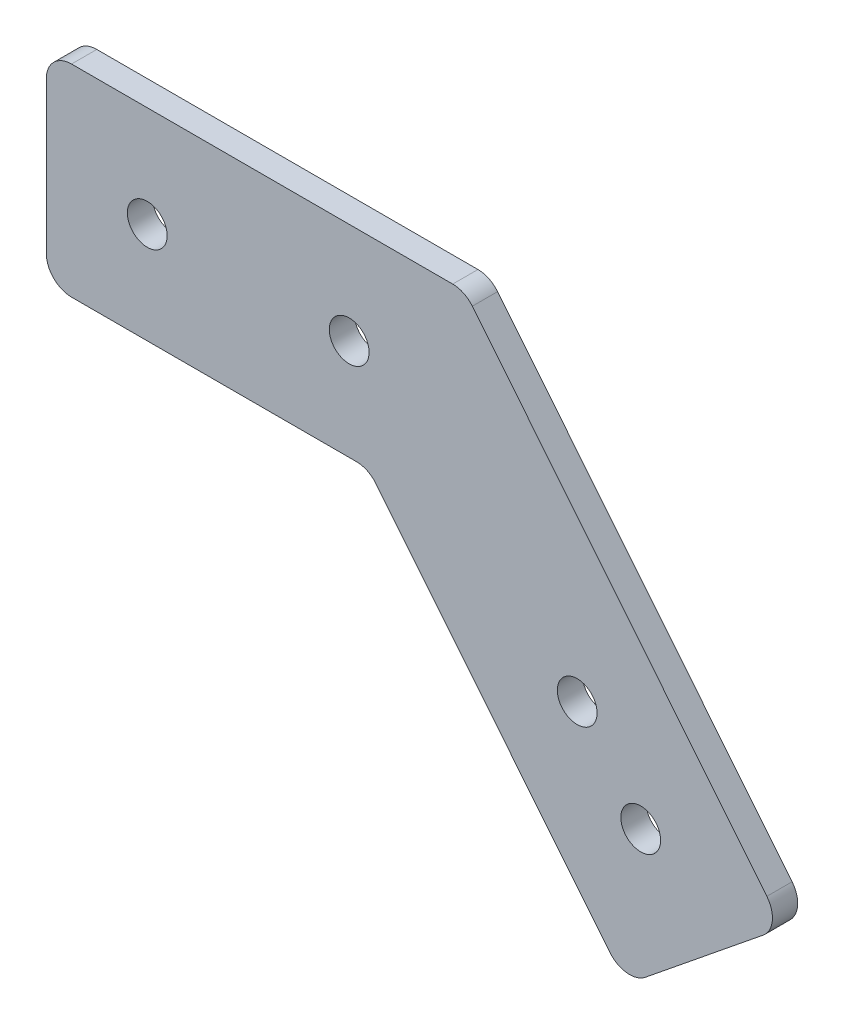
SolidWorks part; units mm, degrees
ref_plane "Front Plane" through (0, 0, 0) normal (0, 0, 1) x (1, 0, 0)
ref_plane "Top Plane" through (0, 0, 0) normal (0, 1, 0) x (1, 0, 0)
ref_plane "Right Plane" through (0, 0, 0) normal (1, 0, 0) x (0, 0, -1)
sketch "Sketch1" plane through (0, 0, 0) normal (0, 0, 1) x (1, 0, 0)
  line L0 (72.8931, 668.9416) -> (92.6349, 684.9236)
  line L1 (50.8, 696.2321) -> (635, -25.4) construction
  line L2 (660.4, -16.4074) -> (50.8, 736.6) construction
  line L3 (92.6349, 684.9236) -> (50.8, 736.6)
  line L4 (50.8, 1244.6) -> (50.8, 0) construction
  line L5 (50.8, 736.6) -> (0, 736.6)
  line L6 (0, 736.6) -> (0, 696.2321)
  line L7 (0, 696.2321) -> (50.8, 696.2321)
  line L8 (50.8, 696.2321) -> (72.8931, 668.9416)
  line L9 (82.764, 676.9326) -> (50.8, 716.416) construction
  line L10 (50.8, 736.6) -> (50.8, 696.2321) construction
  line L11 (50.8, 696.2321) -> (40.5187, 708.9321)
  line L12 (40.5187, 708.9321) -> (0, 708.9321)
  line L13 (0, 734.3321) -> (52.636, 734.3321)
  circle A0 centre (12.7, 721.6321) radius 2.5019
  circle A1 centre (38.1, 721.6321) radius 2.5019
  circle A2 centre (66.782, 696.6743) radius 2.5019
  circle A3 centre (74.773, 686.8034) radius 2.5019
  dimension "D1" = 25.4
  dimension "D5" = 5.0038
  dimension "D2" = 12.7
  dimension "D3" = 12.7
  dimension "D4" = 25.4
  dimension "D6" = 12.7
  dimension "D7" = 25.4
  dimension "D8" = 12.7
  dimension "D9" = 12.7
extrude "Boss-Extrude1" add sketch "Sketch1" along normal blind 3.175
fillet "Fillet1" radius 3.175 6 edges at (0, 708.9321, 1.5875) (40.5187, 708.9321, 1.5875) (72.8931, 668.9416, 1.5875) (92.6349, 684.9236, 1.5875) (52.636, 734.3321, 1.5875) (0, 734.3321, 1.5875)
equation "\"Thick\"= \"in\""
